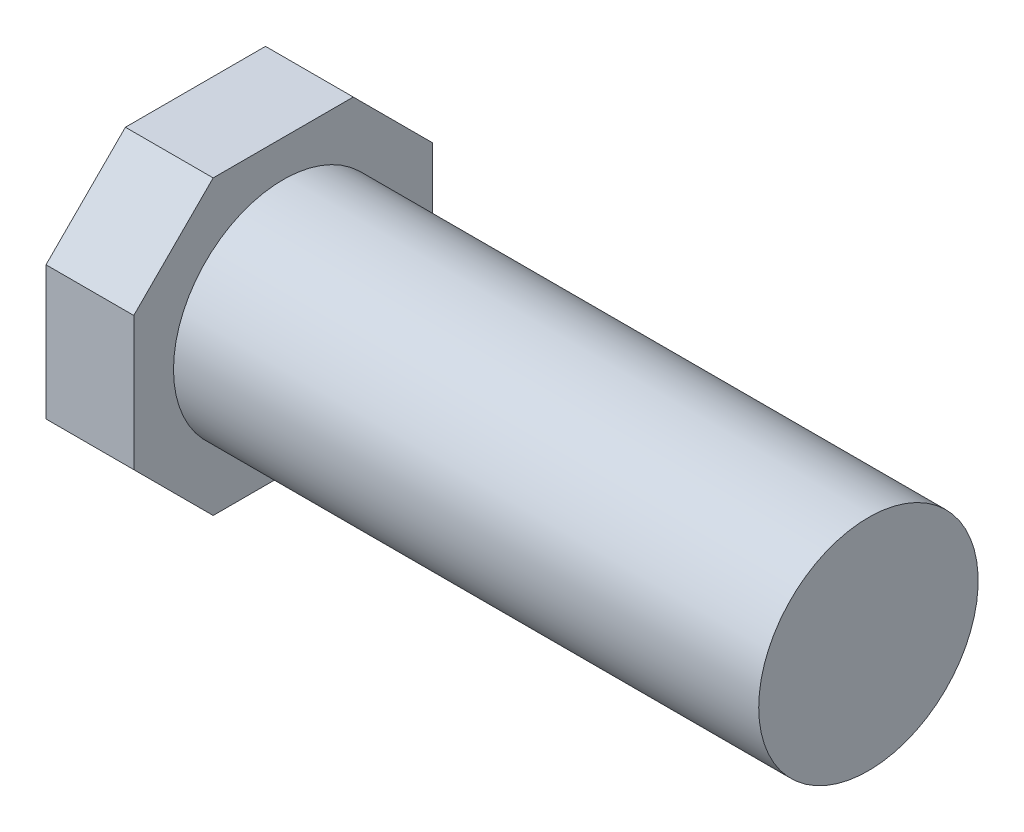
SolidWorks part; units mm, degrees
ref_plane "Front Plane" through (0, 0, 0) normal (0, 0, 1) x (1, 0, 0)
ref_plane "Top Plane" through (0, 0, 0) normal (0, 1, 0) x (1, 0, 0)
ref_plane "Right Plane" through (0, 0, 0) normal (1, 0, 0) x (0, 0, -1)
sketch "Sketch1" plane through (65.9692, 0, 0) normal (-1, 0, 0) x (0, 0, 1)
  circle A0 centre (-5.3448, 7.7856) radius 3.75
  dimension "D1" = 7.5
extrude "Boss-Extrude1" add sketch "Sketch1" along normal blind 14 and the other way blind 9
sketch "Sketch2" plane through (51.9692, 0, 0) normal (-1, 0, 0) x (0, 0, 1)
  line L5 (-9.0948, 11.4259) -> (-7.7389, 12.7818)
  line L6 (-1.5948, 11.4259) -> (-2.9506, 12.7818)
  line L7 (-1.5948, 11.4259) -> (-0.2371, 10.0683)
  line L8 (-9.0948, 11.4259) -> (-10.4524, 10.0683)
  line L9 (-9.0948, 4.1453) -> (-7.7389, 2.7895)
  line L10 (-7.7389, 2.7895) -> (-2.9506, 2.7895)
  line L11 (-2.9506, 2.7895) -> (-1.5948, 4.1453)
  line L12 (-7.7389, 12.7818) -> (-2.9506, 12.7818)
  line L13 (-1.5948, 4.1453) -> (-0.2371, 5.503)
  line L14 (-0.2371, 5.503) -> (-0.2371, 10.0683)
  line L15 (-9.0948, 4.1453) -> (-10.4524, 5.503)
  line L16 (-10.4524, 5.503) -> (-10.4524, 10.0683)
  dimension "D1" = 1.9175
  dimension "D2" = 1.92
extrude "Boss-Extrude2" add sketch "Sketch2" against normal blind 3
